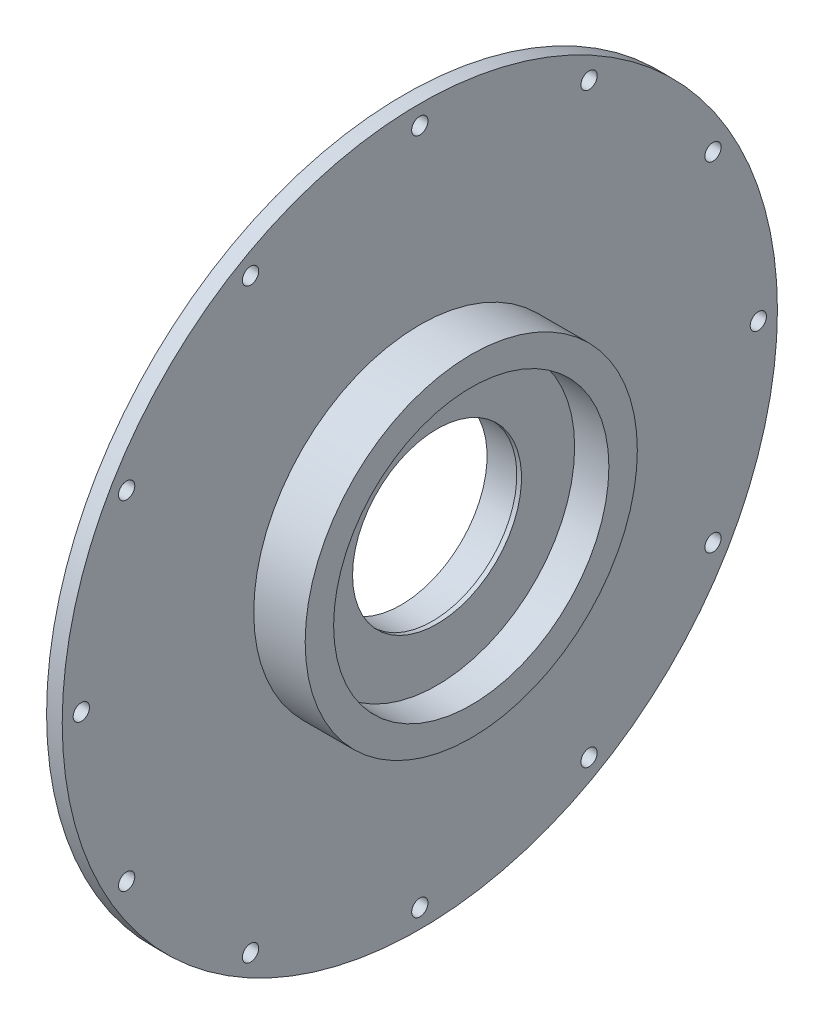
SolidWorks part; units mm, degrees
ref_plane "Front Plane" through (0, 0, 0) normal (0, 0, 1) x (1, 0, 0)
ref_plane "Top Plane" through (0, 0, 0) normal (0, 1, 0) x (1, 0, 0)
ref_plane "Right Plane" through (0, 0, 0) normal (1, 0, 0) x (0, 0, -1)
sketch "Sketch1" plane through (0, 0, 0) normal (0, 0, 1) x (1, 0, 0)
  line L0 (0, 0) -> (47.5556, 0) construction
  line L1 (0, 27.5) -> (10, 27.5)
  line L2 (0, 0) -> (0, 77.5819) construction
  line L3 (0.5, 102.5) -> (2.5, 102.5)
  line L4 (0.5, 102.5) -> (-0.5, 102.2)
  line L5 (2.5, 102.5) -> (2.5, 104)
  line L6 (2.5, 104) -> (1, 104)
  line L7 (1, 104) -> (1, 114.3)
  line L8 (-0.5, 102.2) -> (-0.5, 100.5)
  line L9 (-0.5, 100.5) -> (2.5, 100.5)
  line L10 (2.5, 100.5) -> (5, 98.23)
  line L11 (2.5, 102.5) -> (2.5, 100.5) construction
  line L12 (0, 27.5) -> (0, 35.2295)
  line L13 (10, 27.5) -> (10, 27)
  line L14 (10, 27) -> (11.5, 27)
  line L15 (5, 98.23) -> (5, 73.23)
  line L17 (11.5, 27) -> (11.5, 43.989)
  line L18 (11.5, 43.989) -> (22.4364, 43.989)
  line L19 (22.4364, 43.989) -> (22.4364, 53.084)
  line L20 (22.4364, 53.084) -> (6, 53.084)
  line L21 (5, 73.23) -> (0, 35.2295)
  line L22 (6, 114.3) -> (1, 114.3)
  line L24 (6, 53.084) -> (6, 114.3)
  point P19 (1, 114.3)
  point P21 (0, 0)
  point P26 (6, 114.1954)
  dimension "D1" = 10
  dimension "D2" = 27.5
  dimension "D3" = 75
  dimension "D4" = 2.5
  dimension "D5" = 2
  dimension "D6" = 0.3
  dimension "D7" = 1
  dimension "D8" = 1.5
  dimension "D10" = 1.7
  dimension "D11" = 2.5
  dimension "D12" = 2.27
  dimension "D13" = 0.5
  dimension "D14" = 25
  dimension "D16" = 1.5
  dimension "D17" = 114.3
  dimension "D18" = 5
revolve "Revolve1" add sketch "Sketch1" angle 360 about L0
sketch "Sketch2" plane through (0, 0, 0) normal (1, 0, 0) x (0, 0, -1)
  line L0 (0, 0) -> (0, 102.2) construction
  line L1 (0, 102.2) -> (0, 105.4) construction
  line L2 (0, 105.4) -> (0, 108.2) construction
  circle A0 centre (0, 0) radius 102.2 construction
  circle A2 centre (0, 108.2) radius 2.6
  circle A3 centre (54.1, 93.7039) radius 2.6
  circle A4 centre (93.7039, 54.1) radius 2.6
  circle A5 centre (108.2, 0) radius 2.6
  circle A6 centre (93.7039, -54.1) radius 2.6
  circle A7 centre (54.1, -93.7039) radius 2.6
  circle A8 centre (0, -108.2) radius 2.6
  circle A9 centre (-54.1, -93.7039) radius 2.6
  circle A10 centre (-93.7039, -54.1) radius 2.6
  circle A11 centre (-108.2, 0) radius 2.6
  circle A12 centre (-93.7039, 54.1) radius 2.6
  circle A13 centre (-54.1, 93.7039) radius 2.6
  point P34 (0, 0)
  dimension "D3" = 5.2
  dimension "D1" = 3.2
  dimension "D2" = 2.8
  dimension "D4" = 12
extrude "Cut-Extrude1" cut sketch "Sketch2" along normal blind 10
